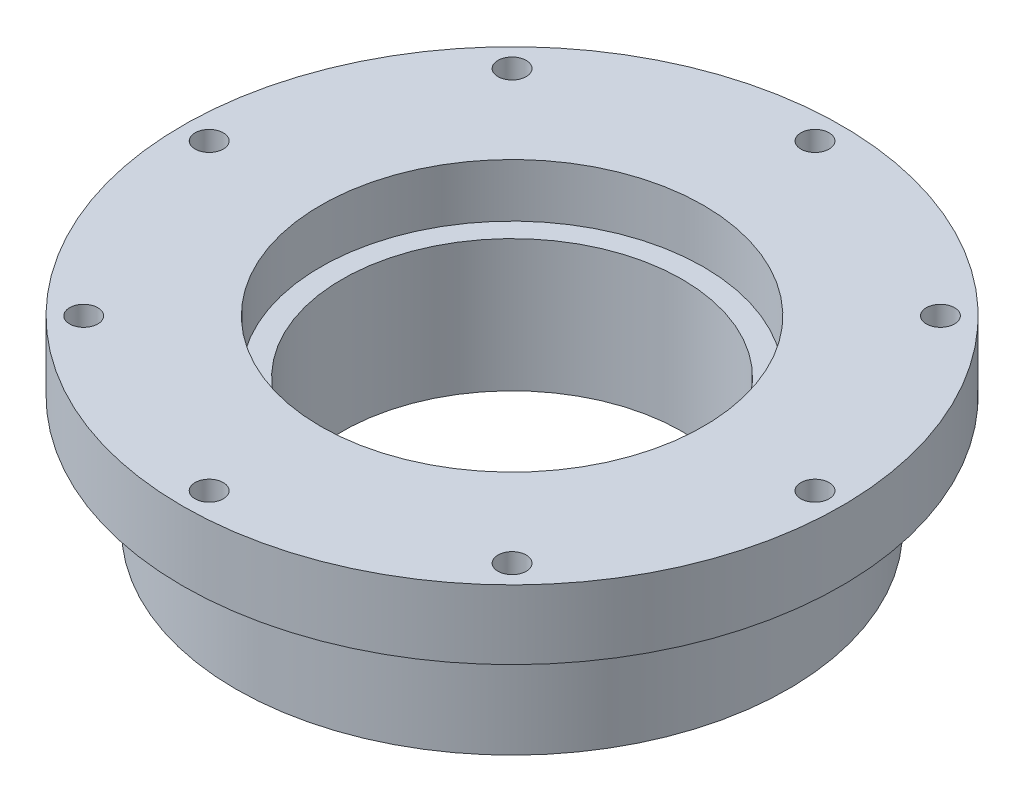
SolidWorks part; units mm, degrees
ref_plane "Front Plane" through (0, 0, 0) normal (0, 0, 1) x (1, 0, 0)
ref_plane "Top Plane" through (0, 0, 0) normal (0, 1, 0) x (1, 0, 0)
ref_plane "Right Plane" through (0, 0, 0) normal (1, 0, 0) x (0, 0, -1)
sketch "Sketch1" plane through (0, 0, 0) normal (0, 1, 0) x (1, 0, 0)
  circle A0 centre (0, 0) radius 55.88
  dimension "D1" = 111.76
extrude "Boss-Extrude1" add sketch "Sketch1" along normal blind 23.495
sketch "Sketch2" plane through (0, 23.495, 0) normal (0, 1, 0) x (1, 0, 0)
  circle A0 centre (0, 0) radius 66.675
  dimension "D1" = 133.35
extrude "Boss-Extrude2" add sketch "Sketch2" along normal blind 13.97
fillet "Fillet1" radius 7.62 1 edges at (0, 23.495, 55.88)
sketch "Sketch3" plane through (0, 37.465, 0) normal (0, 1, 0) x (1, 0, 0)
  line L0 (0, 0) -> (66.675, 0) construction
  line L1 (0, 66.675) -> (0, 0) construction
  circle A0 centre (0, 0) radius 66.675 construction
  circle A1 centre (0, 61.2775) radius 2.8575
  dimension "D1" = 5.715
  dimension "D2" = 5.3975
extrude "Cut-Extrude1" cut sketch "Sketch3" against normal through all
pattern_circular "CirPattern1" count 8 over 360 about axis through (0, 0, 0) along (0, 1, 0) of "Cut-Extrude1"
sketch "Sketch4" plane through (0, 37.465, 0) normal (0, 1, 0) x (1, 0, 0)
  circle A0 centre (0, 0) radius 53.975
  circle A1 centre (0, 0) radius 66.675 construction
  circle A2 centre (0, 0) radius 38.735
  dimension "D1" = 12.7
  dimension "D2" = 15.24
extrude "Cut-Extrude2" cut sketch "Sketch4" against normal blind 10.795 contours A2
sketch "Sketch5" plane through (0, 26.67, 0) normal (0, 1, 0) x (1, 0, 0)
  circle A0 centre (0, 0) radius 34.4043
  dimension "D1" = 68.8086
extrude "Cut-Extrude3" cut sketch "Sketch5" against normal blind 40.894
